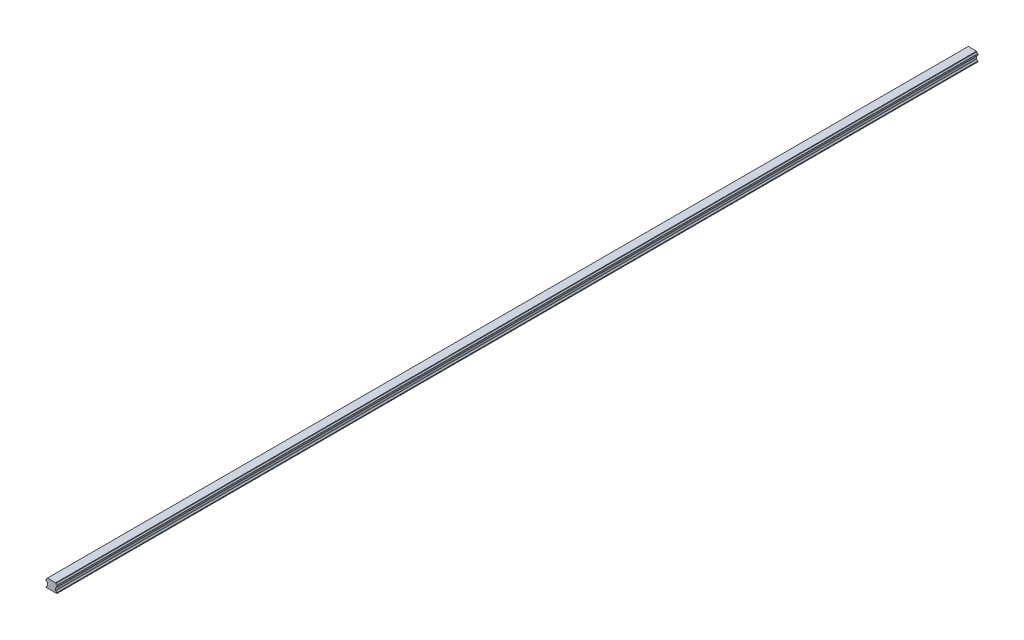
SolidWorks part; units mm, degrees
ref_plane "Piano frontale" through (0, 0, 0) normal (0, 0, 1) x (1, 0, 0)
ref_plane "Piano superiore" through (0, 0, 0) normal (0, 1, 0) x (1, 0, 0)
ref_plane "Piano destro" through (0, 0, 0) normal (1, 0, 0) x (0, 0, -1)
sketch "Schizzo1" plane through (0, 0, 0) normal (0, 0, 1) x (1, 0, 0)
  line L0 (-10.0012, -16.2762) -> (-7.5012, -13.7762)
  line L1 (-7.5012, -13.7762) -> (-7.5012, -8.7762)
  line L2 (-7.5012, -8.7762) -> (-8.0088, -8.2686)
  line L3 (-10.3066, -5.9708) -> (-10.5012, -5.7762)
  line L4 (-10.5012, -5.7762) -> (-10.5012, -2.7762)
  line L5 (-10.5012, -2.7762) -> (-10.3066, -2.5816)
  line L6 (-8.0088, -0.2838) -> (-7.5012, 0.2238)
  line L7 (-7.5012, 0.2238) -> (9.4988, 0.2238)
  line L8 (9.4988, 0.2238) -> (10.0064, -0.2838)
  line L9 (12.3042, -2.5816) -> (12.4988, -2.7762)
  line L10 (12.4988, -2.7762) -> (12.4988, -5.7762)
  line L11 (12.4988, -5.7762) -> (12.3042, -5.9708)
  line L12 (10.0064, -8.2686) -> (9.4988, -8.7762)
  line L13 (9.4988, -8.7762) -> (9.4988, -13.7762)
  line L14 (9.4988, -13.7762) -> (11.9988, -16.2762)
  line L17 (-10.0012, -16.2762) -> (-10.0012, -17.7762)
  line L18 (-10.0012, -17.7762) -> (11.9988, -17.7762)
  line L19 (11.9988, -17.7762) -> (11.9988, -16.2762)
  arc A0 (-8.0088, -8.2686) -> (-10.3066, -5.9708) centre (-10.5012, -8.4632) ccw
  arc A1 (-10.3066, -2.5816) -> (-8.0088, -0.2838) centre (-10.5012, -0.0892) ccw
  arc A2 (10.0064, -0.2838) -> (12.3042, -2.5816) centre (12.4988, -0.0892) ccw
  arc A3 (12.3042, -5.9708) -> (10.0064, -8.2686) centre (12.4988, -8.4632) ccw
  dimension "D1" = 18
extrude "Estrusione-Estrusione1" add sketch "Schizzo1" along normal blind 1900
